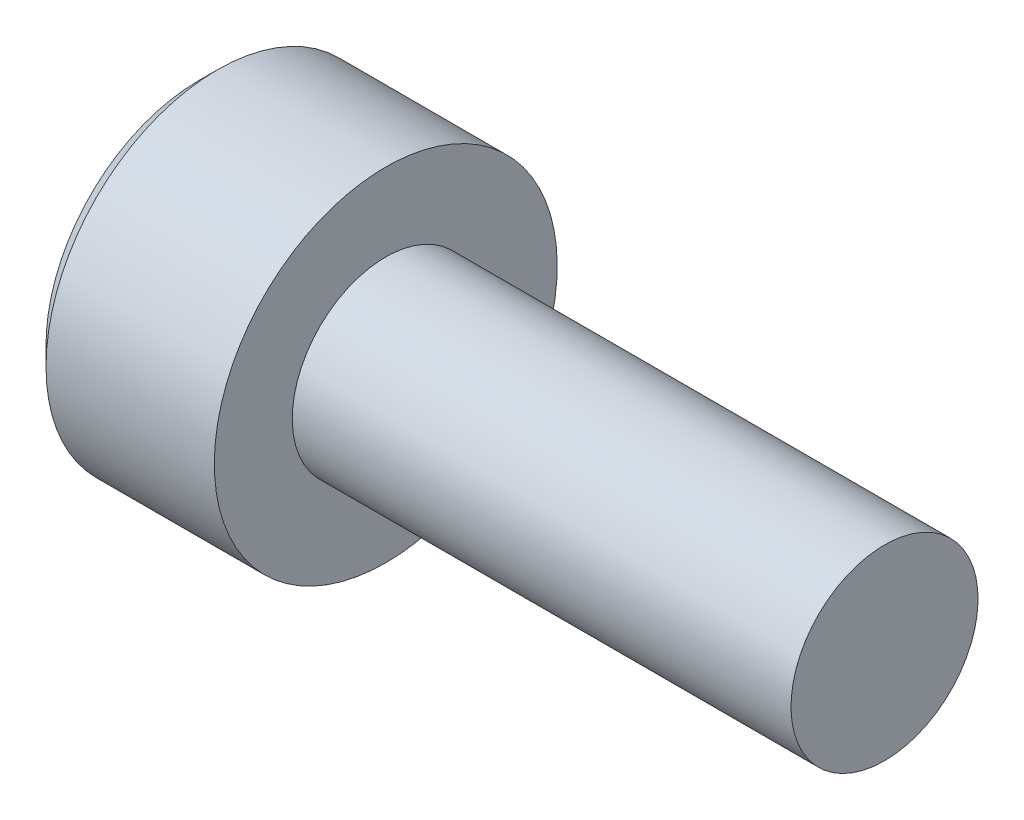
SolidWorks part; units mm, degrees
material "相当于SUS304"
ref_plane "Front Plane" through (0, 0, 0) normal (0, 0, 1) x (1, 0, 0)
ref_plane "Top Plane" through (0, 0, 0) normal (0, 1, 0) x (1, 0, 0)
ref_plane "Right Plane" through (0, 0, 0) normal (1, 0, 0) x (0, 0, -1)
sketch "Sketch1" plane through (0, 0, 0) normal (0, 0, 1) x (1, 0, 0)
  line L0 (-3, 0) -> (8, 0) construction
  line L1 (0, 1.5) -> (8, 1.5)
  line L3 (-3, 0) -> (8, 0)
  line L4 (8, 1.5) -> (8, 0)
  line L6 (0, 1.5) -> (0, 2.75)
  line L7 (0, 2.75) -> (-3, 2.75)
  line L8 (-3, 0) -> (-3, 2.75)
  dimension "L" = 8
  dimension "M" = 3
  dimension "E" = 3
  dimension "A" = 5.5
revolve "Revolve1" add sketch "Sketch1" about L0
cosmetic thread "Thread1" parameters "L_s"=8, "ATD"=2.459
sketch "Sketch2" plane through (0, 0, 0) normal (0, 0, 1) x (1, 0, 0)
  line L0 (-3, 0) -> (-0.9489, 0) construction
  line L1 (-3, 0) -> (8, 0) construction
  line L2 (-0.9489, 0) -> (-1.7, 1.25)
  line L3 (-1.7, 1.25) -> (-3, 1.25)
  line L4 (-3, 0) -> (-3, 2.75) construction
  line L5 (-3, 1.25) -> (-3, 0)
  line L6 (-3, 0) -> (-0.9489, 0)
  dimension "MSM_1" = 1.3
  dimension "FIX_2" = 59
revolve "Cut-Revolve1" cut sketch "Sketch2" about L0
sketch "Sketch3" plane through (-3, 0, 0) normal (-1, 0, 0) x (0, 0, 1)
  line L0 (0, -3.025) -> (0, 3.025) construction
  line L1 (1.25, 0.7217) -> (0, 1.4434)
  line L2 (0, 1.4434) -> (-1.25, 0.7217)
  line L3 (-1.25, 0.7217) -> (-1.25, -0.7217)
  line L4 (-1.25, -0.7217) -> (0, -1.4434)
  line L5 (0, -1.4434) -> (1.25, -0.7217)
  line L6 (1.25, -0.7217) -> (1.25, 0.7217)
  circle A0 centre (0, 0) radius 1.25 construction
extrude "Cut-Extrude1" cut sketch "Sketch3" against normal blind 1.3
chamfer "Chamfer1" distance 0.3 1 edges at (-3, -2.75, 0)
